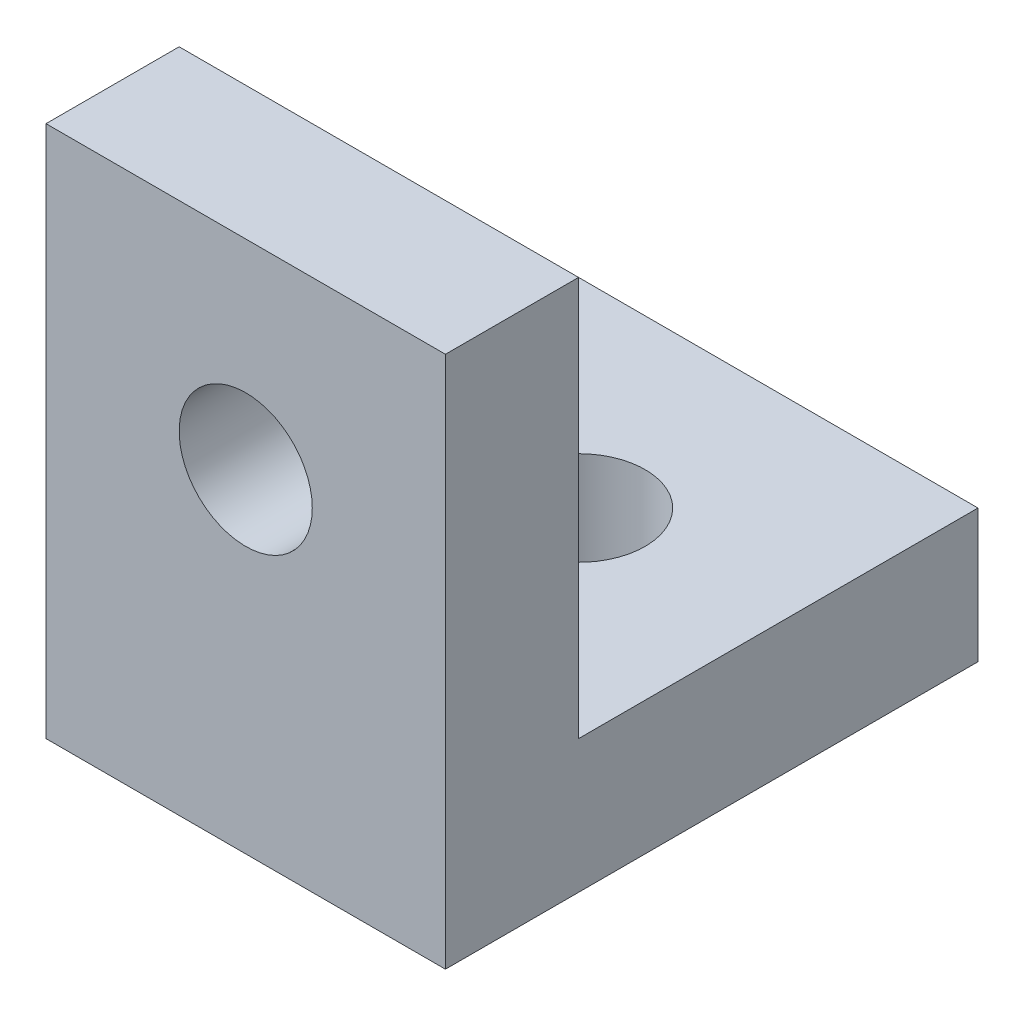
SolidWorks part; units mm, degrees
ref_plane "Front Plane" through (0, 0, 0) normal (0, 0, 1) x (1, 0, 0)
ref_plane "Top Plane" through (0, 0, 0) normal (0, 1, 0) x (1, 0, 0)
ref_plane "Right Plane" through (0, 0, 0) normal (1, 0, 0) x (0, 0, -1)
sketch "Sketch1" plane through (0, 0, 0) normal (0, 1, 0) x (1, 0, 0)
  line L1 (0, 0) -> (30, 0)
  line L2 (0, 0) -> (0, 30)
  line L3 (0, 30) -> (30, 30)
  line L4 (30, 0) -> (30, 30)
  dimension "D1" = 30
  dimension "D2" = 30
extrude "Boss-Extrude1" add sketch "Sketch1" along normal blind 10
sketch "Sketch4" plane through (0, 0, 0) normal (0, 0, 1) x (1, 0, 0)
  line L1 (0, 0) -> (30, 0)
  line L2 (0, 0) -> (0, 40)
  line L3 (0, 40) -> (30, 40)
  line L4 (30, 0) -> (30, 40)
  dimension "D1" = 40
  dimension "D2" = 30
extrude "Boss-Extrude2" add sketch "Sketch4" along normal blind 10
sketch "Sketch5" plane through (0, 0, 10) normal (0, 0, 1) x (1, 0, 0)
  line L0 (0, 0) -> (30, 0) construction
  circle A0 centre (15, 25) radius 5
  dimension "D1" = 10
  dimension "D2" = 25
  dimension "D3" = 15
extrude "Cut-Extrude1" cut sketch "Sketch5" against normal blind 10
sketch "Sketch6" plane through (0, 10, 0) normal (0, 1, 0) x (1, 0, 0)
  circle A0 centre (15, 15) radius 5
  dimension "D1" = 10
  dimension "D2" = 15
  dimension "D3" = 15
extrude "Cut-Extrude2" cut sketch "Sketch6" against normal blind 10
